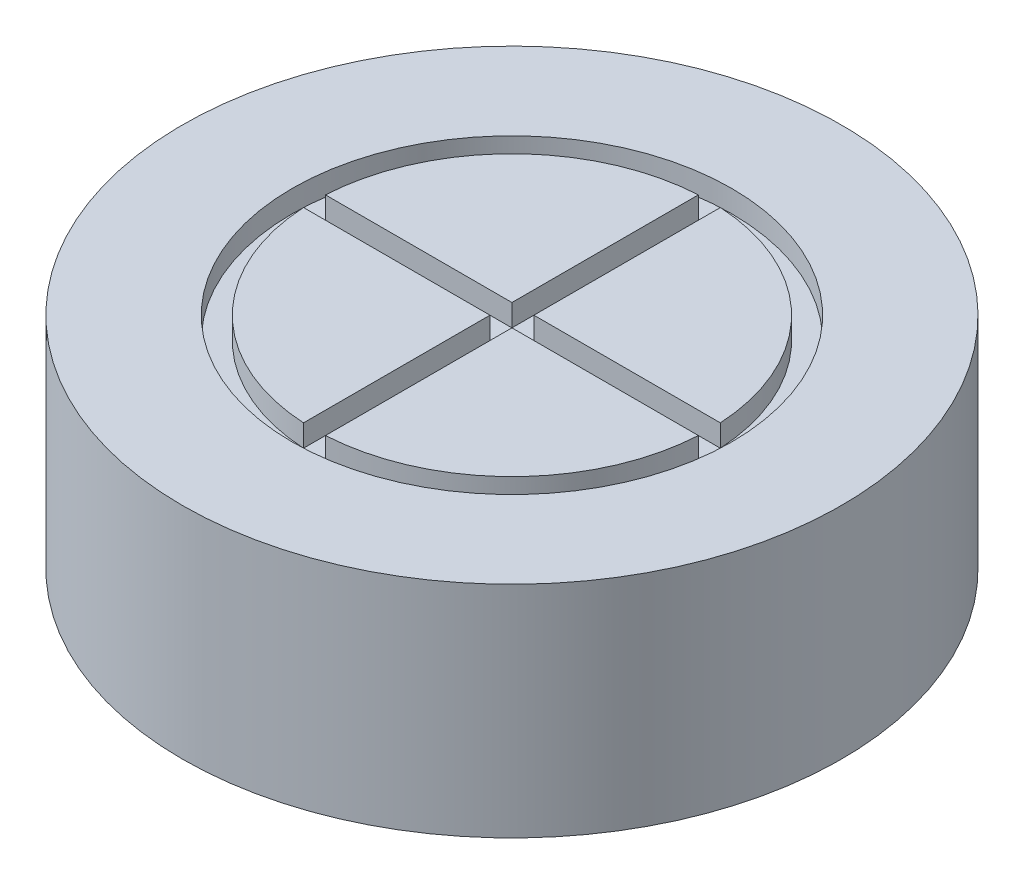
SolidWorks part; units mm, degrees
ref_plane "Front Plane" through (0, 0, 0) normal (0, 0, 1) x (1, 0, 0)
ref_plane "Top Plane" through (0, 0, 0) normal (0, 1, 0) x (1, 0, 0)
ref_plane "Right Plane" through (0, 0, 0) normal (1, 0, 0) x (0, 0, -1)
sketch "Sketch1" plane through (0, 0, 0) normal (0, 1, 0) x (1, 0, 0)
  circle A0 centre (0, 0) radius 15
extrude "Boss-Extrude1" add sketch "Sketch1" along normal blind 10
ref_plane "Plane1" through (0, 10, 0) normal (0, 1, 0) x (1, 0, 0)
sketch "Sketch2" plane through (0, 10, 0) normal (0, 1, 0) x (1, 0, 0)
  line L0 (-0.5, -0.4998) -> (-0.5, -8.9861)
  line L1 (-0.5, -0.4998) -> (-8.9861, -0.4998)
  line L2 (0.4998, 8.9861) -> (0.4998, 0.4998)
  line L3 (-0.5, 8.9861) -> (-0.5, 0.4998)
  line L4 (-8.9861, 0.4998) -> (-0.5, 0.4998)
  line L5 (8.9861, -0.4998) -> (0.4998, -0.4998)
  line L6 (0.4998, -0.4998) -> (0.4998, -8.9861)
  line L7 (0.4998, 0.4998) -> (8.9861, 0.4998)
  circle A0 centre (0, 0) radius 10
  arc A1 (-0.5, 8.9861) -> (-8.9861, 0.4998) centre (0, 0) ccw
  arc A2 (8.9861, 0.4998) -> (0.4998, 8.9861) centre (0, 0) ccw
  arc A3 (0.4998, -8.9861) -> (8.9861, -0.4998) centre (0, 0) ccw
  arc A4 (-8.9861, -0.4998) -> (-0.5, -8.9861) centre (0, 0) ccw
  dimension "D1" = 18
  dimension "D2" = 20
ref_plane "Plane2" through (0, 0, 0) normal (0, -1, 0) x (-1, 0, 0)
sketch "Sketch3" plane through (0, 0, 0) normal (0, -1, 0) x (-1, 0, 0)
  line L0 (0, 5) -> (0, -5)
  arc A0 (0, -5) -> (0, 5) centre (0, 0) ccw
revolve "Cut-Revolve1" cut sketch "Sketch3" angle 360 about L0
extrude "Cut-Extrude1" cut sketch "Sketch2" against normal blind 1
